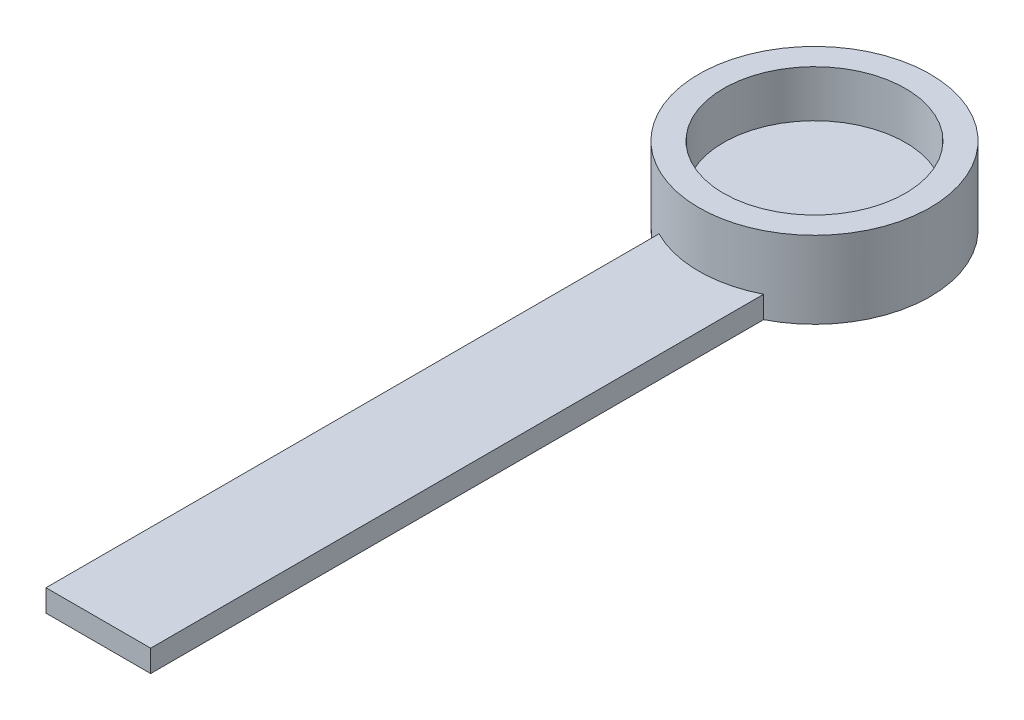
SolidWorks part; units mm, degrees
ref_plane "Front Plane" through (0, 0, 0) normal (0, 0, 1) x (1, 0, 0)
ref_plane "Top Plane" through (0, 0, 0) normal (0, 1, 0) x (1, 0, 0)
ref_plane "Right Plane" through (0, 0, 0) normal (1, 0, 0) x (0, 0, -1)
sketch "0.1mm fit for pot" plane through (0, 0, 0) normal (0, 1, 0) x (1, 0, 0)
  circle A1 centre (0, 0) radius 10.5
  dimension "D2" = 21
extrude "Boss-Extrude1" add sketch "0.1mm fit for pot" along normal blind 2.75
sketch "Sketch4" plane through (0, 2.75, 0) normal (0, 1, 0) x (1, 0, 0)
  circle A0 centre (0, 0) radius 8.25
  circle A1 centre (0, 0) radius 10.5 construction
  circle A2 centre (0, 0) radius 10.5
  dimension "D1" = 16.5
extrude "Boss-Extrude2" add sketch "Sketch4" along normal blind 4.25
sketch "Sketch5" plane through (0, 2.75, 0) normal (0, 1, 0) x (1, 0, 0)
  line L6 (-1, -8.1892) -> (-1, -7.05)
  line L7 (-1, -7.05) -> (1, -7.05)
  line L8 (1, -7.05) -> (1, -8.1892)
  circle A0 centre (0, 0) radius 8.25 construction
  arc A1 (-1, -8.1892) -> (1, -8.1892) centre (0, 0) ccw
  point P3 (0, -8.25)
  point P6 (0, -8.25)
  point P7 (0, -8.25)
extrude "Boss-Extrude3" add sketch "Sketch5" along normal blind 2
fillet "Fillet1" radius 0.25 5 edges at (-1, 4.75, 7.6196) (1, 4.75, 7.6196) (1, 3.75, 7.05) (0, 4.75, 7.05) (-1, 3.75, 7.05)
sketch "Sketch6" plane through (0, 0, 0) normal (0, -1, 0) x (1, 0, 0)
  line L1 (-4.75, 9.3642) -> (-4.75, 65)
  line L2 (-4.75, 65) -> (4.75, 65)
  line L3 (4.75, 65) -> (4.75, 9.3642)
  circle A0 centre (0, 0) radius 10.5 construction
  arc A1 (4.75, 9.3642) -> (-4.75, 9.3642) centre (0, 0) ccw
  point P5 (0, 0)
extrude "Boss-Extrude4" add sketch "Sketch6" against normal blind 2
